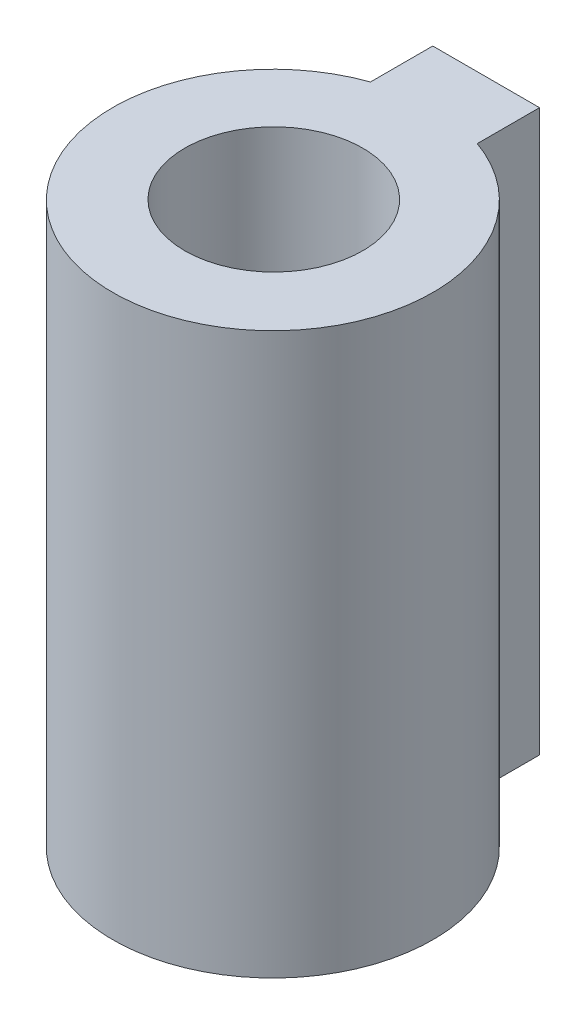
SolidWorks part; units mm, degrees
material "Plain Carbon Steel"
ref_plane "Front Plane" through (0, 0, 0) normal (0, 0, 1) x (1, 0, 0)
ref_plane "Top Plane" through (0, 0, 0) normal (0, 1, 0) x (1, 0, 0)
ref_plane "Right Plane" through (0, 0, 0) normal (1, 0, 0) x (0, 0, -1)
sketch "Sketch1" plane through (0, 0, 0) normal (0, 1, 0) x (1, 0, 0)
  line L0 (-10.0485, 7.218) -> (-10.0485, 22.5656) construction
  line L7 (-7.0485, 15.7033) -> (-7.0485, 19.2033)
  line L8 (-7.0485, 19.2033) -> (-13.0485, 19.2033)
  line L9 (-13.0485, 15.7033) -> (-13.0485, 19.2033)
  line L10 (-7.0485, 15.7033) -> (-13.0485, 19.2033) construction
  line L11 (-7.0485, 19.2033) -> (-13.0485, 15.7033) construction
  circle A0 centre (-10.0485, 7.218) radius 9
  point P2 (-10.0485, 14.6727)
  point P4 (-10.0485, 17.4533)
  dimension "D1" = 18
  dimension "D2" = 6
  dimension "D3" = 3.5
extrude "Boss-Extrude1" add sketch "Sketch1" along normal blind 31.5
sketch "Sketch4" plane through (0, 31.5, 0) normal (0, 1, 0) x (1, 0, 0)
  line L0 (-10.0485, 19.2033) -> (-10.0485, -4.6628) construction
  line L1 (-7.0485, 19.2033) -> (-13.0485, 19.2033) construction
  line L2 (-10.0485, 7.2702) -> (5.4952, 7.2702) construction
sketch "Sketch5" plane through (0, 31.5, 0) normal (0, 1, 0) x (1, 0, 0)
  circle A0 centre (-10.0485, 7.2702) radius 5
  dimension "D1" = 10
extrude "Cut-Extrude1" cut sketch "Sketch5" against normal blind 25
